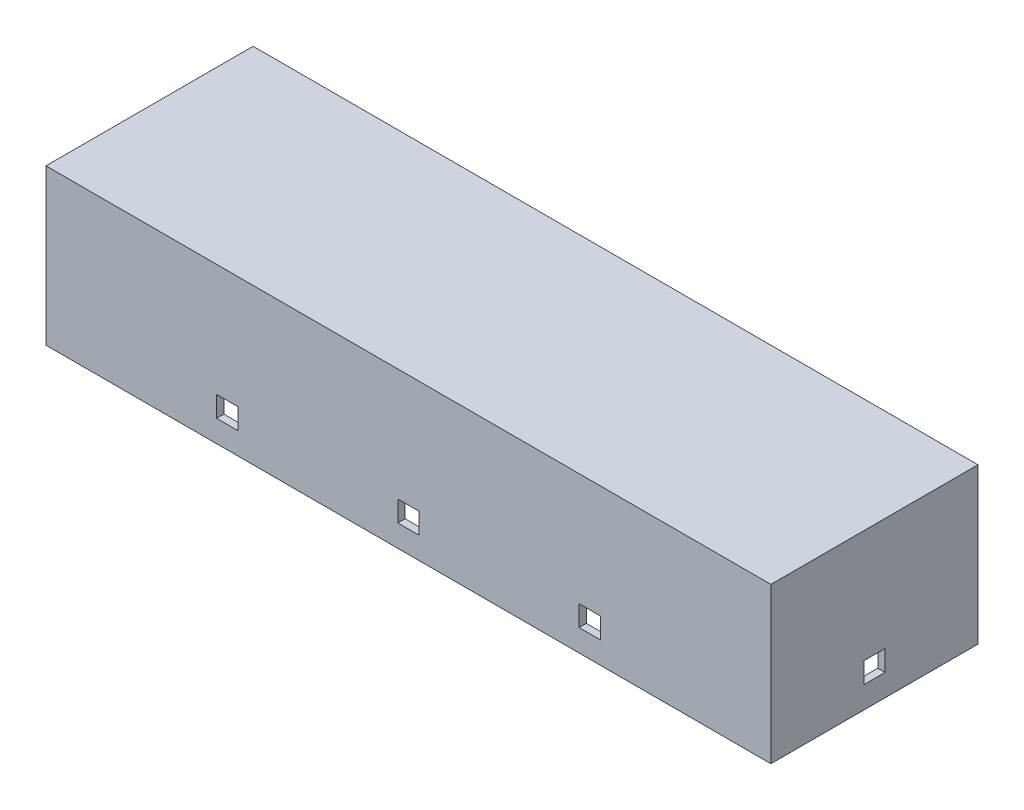
SolidWorks part; units mm, degrees
ref_plane "Front Plane" through (0, 0, 0) normal (0, 0, 1) x (1, 0, 0)
ref_plane "Top Plane" through (0, 0, 0) normal (0, 1, 0) x (1, 0, 0)
ref_plane "Right Plane" through (0, 0, 0) normal (1, 0, 0) x (0, 0, -1)
sketch "Sketch1" plane through (0, 0, 0) normal (0, 1, 0) x (1, 0, 0)
  line L1 (-70, -20) -> (70, -20)
  line L2 (-70, -20) -> (-70, 20)
  line L3 (-70, 20) -> (70, 20)
  line L4 (70, -20) -> (70, 20)
  line L5 (-70, -20) -> (70, 20) construction
  line L6 (-70, 20) -> (70, -20) construction
  point P0 (0, 0)
  dimension "D1" = 140
  dimension "D2" = 40
extrude "Boss-Extrude1" add sketch "Sketch1" along normal blind 30
sketch "Sketch2" plane through (0, 0, 0) normal (0, -1, 0) x (1, 0, 0)
  line L0 (-70, 20) -> (70, 20) construction
  line L1 (-68.6, -18.6) -> (68.6, -18.6)
  line L2 (-68.6, -18.6) -> (-68.6, 18.6)
  line L3 (-68.6, 18.6) -> (68.6, 18.6)
  line L4 (68.6, -18.6) -> (68.6, 18.6)
  line L5 (-68.6, -18.6) -> (68.6, 18.6) construction
  line L6 (-68.6, 18.6) -> (68.6, -18.6) construction
  line L7 (-70, -20) -> (-70, 20) construction
  point P0 (0, 0)
  dimension "D1" = 1.4
  dimension "D2" = 1.4
extrude "Cut-Extrude1" cut sketch "Sketch2" against normal blind 28.4
sketch "Sketch3" plane through (-70, 0, 0) normal (-1, 0, 0) x (0, 0, 1)
  line L0 (-2.05, 4.25) -> (2.05, 4.25)
  line L1 (-2.05, 4.25) -> (-2.05, 8.25)
  line L2 (-2.05, 8.25) -> (2.05, 8.25)
  line L3 (2.05, 4.25) -> (2.05, 8.25)
  line L4 (-2.05, 4.25) -> (2.05, 8.25) construction
  line L5 (-2.05, 8.25) -> (2.05, 4.25) construction
  line L6 (-20, 0) -> (20, 0) construction
  point P0 (0, 6.25)
  dimension "D1" = 4
  dimension "D2" = 4.1
  dimension "D3" = 4.25
sketch "Sketch4" plane through (0, 0, 20) normal (0, 0, 1) x (1, 0, 0)
  line L0 (-2.05, 4.25) -> (0, 4.25)
  line L1 (-2.05, 4.25) -> (-2.05, 8.25)
  line L2 (-2.05, 8.25) -> (0, 8.25)
  line L4 (0, 0) -> (0, 11.8012) construction
  line L5 (-37.05, 4.25) -> (-32.95, 4.25)
  line L6 (-70, 0) -> (70, 0) construction
  line L7 (0, 8.25) -> (0, 4.25)
  line L8 (-37.05, 4.25) -> (-37.05, 8.25)
  line L9 (-37.05, 8.25) -> (-32.95, 8.25)
  line L10 (-32.95, 4.25) -> (-32.95, 8.25)
  line L11 (-37.05, 4.25) -> (-32.95, 8.25) construction
  line L12 (-37.05, 8.25) -> (-32.95, 4.25) construction
  line L13 (-70, 30) -> (-70, 0) construction
  point P1 (0, 0)
  point P4 (-35, 6.25)
  dimension "D1" = 4
  dimension "D2" = 2.05
  dimension "D3" = 4.25
  dimension "D4" = 4
  dimension "D5" = 4.1
  dimension "D6" = 4.25
  dimension "D7" = 35
extrude "Cut-Extrude2" cut sketch "Sketch3" against normal through all
extrude "Cut-Extrude3" cut sketch "Sketch4" against normal through all
mirror "Mirror1" about plane through (0, 0, 0) normal (1, 0, 0) of "Cut-Extrude3"
